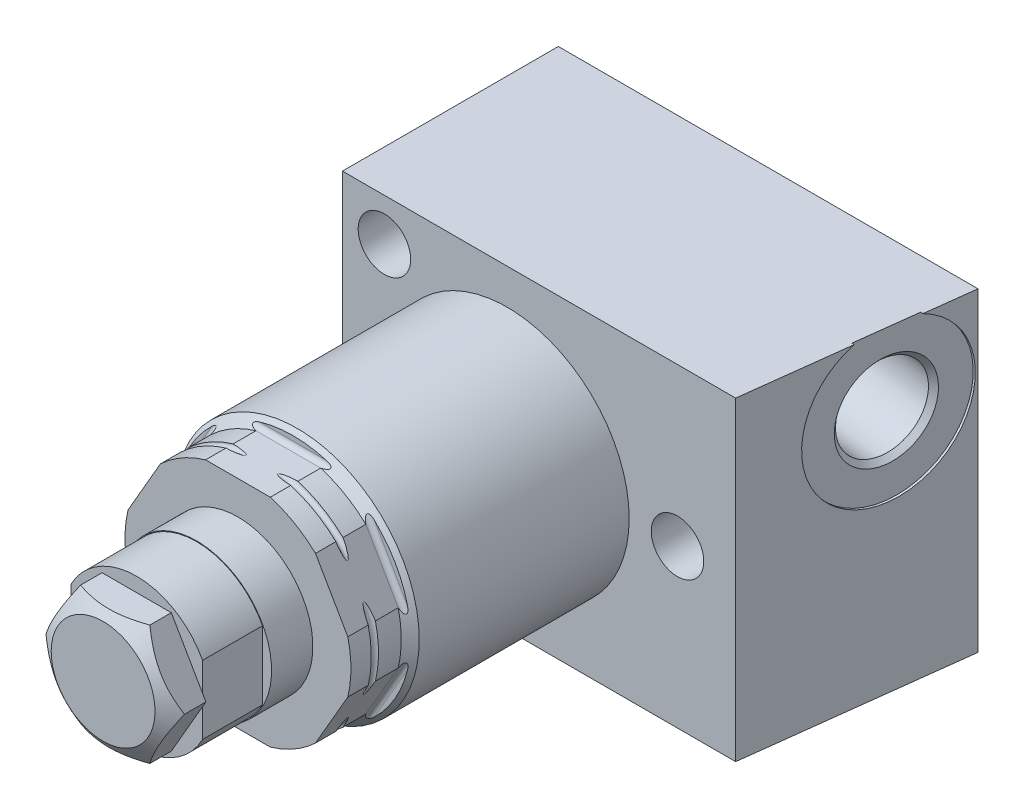
SolidWorks part; units mm, degrees
material "Alloy Steel"
ref_plane "Front Plane" through (0, 0, 0) normal (0, 0, 1) x (1, 0, 0)
ref_plane "Top Plane" through (0, 0, 0) normal (0, 1, 0) x (1, 0, 0)
ref_plane "Right Plane" through (0, 0, 0) normal (1, 0, 0) x (0, 0, -1)
sketch "Sketch1" plane through (0, 0, 0) normal (1, 0, 0) x (0, 0, -1)
  line L0 (0, 0) -> (122.3375, 0) construction
  line L1 (0, 0) -> (0, 11.6713)
  line L6 (0, 11.6713) -> (-7.112, 11.6713)
  line L7 (-7.112, 11.6713) -> (-8.3566, 12.9159)
  line L8 (-8.3566, 12.9159) -> (-35.8267, 12.9159)
  line L9 (-35.8267, 12.9159) -> (-36.7792, 11.9634)
  line L10 (-36.7792, 11.9634) -> (-42.1132, 11.9634)
  line L11 (-42.1132, 11.9634) -> (-42.1132, 0)
  line L12 (0, 0) -> (-42.1132, 0)
  dimension "D5" = 23.3426
  dimension "D6" = 7.112
  dimension "D7" = 25.8318
  dimension "D8" = 45
  dimension "D9" = 42.1132
  dimension "D10" = 23.9268
  dimension "D11" = 45
  dimension "D12" = 5.334
revolve "Revolve1" add sketch "Sketch1" angle 360 about L0
sketch "Sketch2" plane through (0, 0, 0) normal (1, 0, 0) x (0, 0, -1)
  line L0 (0, 0) -> (-47.105, 0) construction
  line L1 (-42.1132, 11.4617) -> (-36.7792, 11.4617)
  line L2 (-42.1132, 11.9634) -> (-42.1132, -11.9634) construction
  line L3 (-36.2712, 11.9697) -> (-36.2712, 14.6367)
  line L4 (-36.2712, 14.6367) -> (-42.1132, 14.6367)
  line L5 (-42.1132, 14.6367) -> (-42.1132, 11.4617)
  arc A0 (-36.2712, 11.9697) -> (-36.7792, 11.4617) centre (-36.7792, 11.9697) cw
  dimension "D4" = 0.508
  dimension "D1" = 22.9235
  dimension "D2" = 5.842
  dimension "D3" = 3.175
extrude "Cut-Extrude1" cut sketch "Sketch2" against normal through all and the other way through all
pattern_circular "CirPattern1" count 6 over 360 about axis through (0, 0, 0) along (0, 0, 1) of "Cut-Extrude1"
sketch "Sketch6" plane through (0, 0, 0) normal (0, 1, 0) x (1, 0, 0)
  line L0 (-17.4498, -13.5932) -> (24.1933, -13.5932)
  line L1 (24.1933, -13.5932) -> (27.0002, 9.2668)
  line L2 (27.0002, 9.2668) -> (-17.4498, 9.2668)
  line L3 (-17.4498, 9.2668) -> (-17.4498, -13.5932)
  line L4 (3.428, -42.1132) -> (-3.428, -42.1132) construction
  dimension "D1" = 28.52
  dimension "D2" = 83
  dimension "D3" = 22.86
  dimension "D4" = 44.45
  dimension "D5" = 17.4498
extrude "Extrude1" add sketch "Sketch6" along normal mid plane 33.3502
sketch "Sketch3" plane through (0, 0, 0) normal (1, 0, 0) x (0, 0, -1)
  line L0 (0, 0) -> (-60.8041, 0) construction
  line L1 (-56.3932, 0) -> (-56.3932, 7.9375) construction
  line L2 (-52.8372, 7.9375) -> (-42.1132, 7.9375)
  line L3 (-42.1132, 2.7621) -> (-42.1132, 8.6996) construction
  line L4 (-42.1132, 7.9375) -> (-42.1132, 0)
  line L5 (-42.1132, 2.7621) -> (-42.1132, -2.7621) construction
  line L6 (-42.1132, 0) -> (-52.8372, 0)
  line L7 (-52.8372, 7.9375) -> (-52.8372, 0)
  line L9 (9.2668, 16.6751) -> (9.2668, -16.6751) construction
  dimension "D1" = 3.556
  dimension "D2" = 15.875
  dimension "D3" = 65.66
revolve "Revolve2" add sketch "Sketch3" angle 360 about L0
sketch "Sketch4" plane through (0, 0, 52.8372) normal (0, 0, 1) x (1, 0, 0)
  circle A0 centre (0, 0) radius 3.0226
  circle A1 centre (0, 0) radius 7.9375 construction
  dimension "D1" = 6.0452
extrude "Cut-Extrude2" cut sketch "Sketch4" against normal blind 8.001
sketch "Sketch5" plane through (0, 0, 0) normal (1, 0, 0) x (0, 0, -1)
  line L0 (-42.1132, 11.4617) -> (-42.1132, 8.6996) construction
  line L1 (0, 0) -> (-52.6213, 0) construction
  line L2 (-39.9542, 15.1384) -> (-39.9542, 11.9634)
  line L3 (-39.1922, 15.1384) -> (-39.1922, 11.9634)
  line L4 (-39.9542, 15.1384) -> (-39.1922, 15.1384)
  arc A0 (-39.9542, 11.9634) -> (-39.1922, 11.9634) centre (-39.5732, 11.9634) ccw
  dimension "D3" = 0.762
  dimension "D1" = 2.54
  dimension "D2" = 11.9634
  dimension "D4" = 3.175
revolve "Cut-Revolve1" cut sketch "Sketch5" angle 360 about L1
hole_wizard "Hole1" positions "Sketch8" profile "Sketch7" legacy end condition up to next
sketch "Sketch8" plane through (0, 0, 13.5932) normal (0, 0, 1) x (1, 0, 0)
  line L0 (0, 0) -> (0, 25.169) construction
  line L1 (0, 0) -> (-25.7102, 0) construction
  point P0 (-13.0048, 12.192)
  point P9 (-13.0048, -12.192)
  point P10 (18.034, 0)
  dimension "D1" = 12.192
  dimension "D2" = 13.0048
  dimension "D3" = 18.034
sketch "Sketch7" plane through (-13.0048, 12.192, 13.5932) normal (1, 0, 0) x (0, -1, 0)
  line L0 (0, 0) -> (0, 22.86)
  line L1 (0, 22.86) -> (2.7813, 22.86)
  line L2 (2.7813, 22.86) -> (2.7813, 0)
  line L3 (2.7813, 0) -> (0, 0)
  line L4 (0, 110) -> (0, -10) construction
  dimension "Diameter" = 5.5626
  dimension "Depth" = 22.86
ref_plane "Plane1" through (0, 9.0932, 0) normal (0, 1, 0) x (-1, 0, 0)
sketch "Sketch9" plane through (0, 9.0932, 0) normal (0, 1, 0) x (-1, 0, 0)
  line L0 (-25.9632, -0.8212) -> (-18.705, -1.7124) construction
  line L1 (-24.1933, 13.5932) -> (-27.0002, -9.2668) construction
  line L2 (-24.9572, 7.3722) -> (-24.7051, 7.3413)
  line L3 (-24.7051, 7.3413) -> (-25.1075, 4.0639)
  line L4 (-25.1075, 4.0639) -> (-24.6431, 3.4695)
  line L5 (-24.6431, 3.4695) -> (-14.6849, 2.2468)
  line L6 (-14.6849, 2.2468) -> (-15.2235, -2.1399)
  line L7 (-15.2235, -2.1399) -> (-25.9632, -0.8212)
  line L8 (-25.9632, -0.8212) -> (-24.9572, 7.3722)
  dimension "D1" = 8.509
  dimension "D2" = 16.51
  dimension "D3" = 0.254
  dimension "D4" = 8.8392
  dimension "D5" = 10.5664
  dimension "D6" = 45
  dimension "D7" = 9.906
revolve "Cut-Revolve2" cut sketch "Sketch9" angle 360 about L0
sketch "Sketch10" plane through (0, 0, 0) normal (0, 1, 0) x (1, 0, 0)
  line L0 (0, 0) -> (0, -56.3853) construction
  line L1 (7.9375, -52.8372) -> (7.9375, -42.1132) construction
  line L2 (6.9723, -52.8372) -> (7.9375, -52.8372)
  line L3 (6.9723, -52.8372) -> (6.9723, -46.4872)
  line L4 (6.9723, -46.4872) -> (7.9375, -46.4872)
  line L5 (7.9375, -52.8372) -> (7.9375, -46.4872)
  line L6 (-7.9375, -52.8372) -> (7.9375, -52.8372) construction
  line L7 (-7.9375, -52.8372) -> (-7.9375, -46.4872)
  line L8 (-6.9723, -46.4872) -> (-7.9375, -46.4872)
  line L9 (-6.9723, -52.8372) -> (-6.9723, -46.4872)
  line L10 (-6.9723, -52.8372) -> (-7.9375, -52.8372)
  dimension "D1" = 13.9446
  dimension "D2" = 6.35
extrude "Cut-Extrude3" cut sketch "Sketch10" against normal through all and the other way through all
sketch "Sketch11" plane through (0, 0, 52.8372) normal (0, 0, 1) x (1, 0, 0)
  line L1 (3.6662, 6.35) -> (-3.6662, 6.35)
  line L2 (-3.6662, 6.35) -> (-7.3323, 0)
  line L3 (-7.3323, 0) -> (-3.6662, -6.35)
  line L4 (-3.6662, -6.35) -> (3.6662, -6.35)
  line L5 (3.6662, -6.35) -> (7.3323, 0)
  line L6 (7.3323, 0) -> (3.6662, 6.35)
  circle A0 centre (0, 0) radius 6.35 construction
  dimension "D1" = 12.7
extrude "Extrude2" add sketch "Sketch11" along normal blind 3.556
sketch "Sketch12" plane through (0, 0, 0) normal (0, 1, 0) x (1, 0, 0)
  line L0 (-7.3323, -55.1095) -> (-7.3323, -56.3932)
  line L1 (-7.3323, -56.3932) -> (-7.3323, -52.8372) construction
  line L2 (-7.3323, -56.3932) -> (-5.4991, -56.3932)
  line L3 (-3.6662, -56.3932) -> (-7.3323, -56.3932) construction
  line L4 (-5.4991, -56.3932) -> (-7.3323, -55.1095)
  line L5 (0, 0) -> (0, -66.9815) construction
  dimension "D1" = 35
  dimension "D2" = 10.9982
revolve "Cut-Revolve3" cut sketch "Sketch12" angle 360 about L5
sketch "Sketch13" plane through (0, 0, -9.2668) normal (0, 0, -1) x (-1, 0, 0)
  circle A0 centre (-17.4752, -9.7155) radius 6.35
  dimension "D1" = 12.7
  dimension "D2" = 17.4752
  dimension "D3" = 9.7155
extrude "Cut-Extrude4" cut sketch "Sketch13" against normal blind 2.54
hole_wizard "Hole2" positions "Sketch15" profile "Sketch14" legacy
sketch "Sketch15" plane through (0, 0, -6.7268) normal (0, 0, -1) x (-1, 0, 0)
  circle A0 centre (-17.4752, -9.7155) radius 6.35 construction
  point P0 (-17.4752, -9.7155)
sketch "Sketch14" plane through (17.4752, -9.7155, -6.7268) normal (1, 0, 0) x (0, 1, 0)
  line L0 (0, 0) -> (0, 14.2676)
  line L1 (0, 14.2676) -> (3.4544, 12.192)
  line L2 (3.4544, 12.192) -> (3.4544, 0)
  line L4 (3.4544, 0) -> (0, 0)
  line L6 (0, 14.2676) -> (-3.4544, 12.192) construction
  line L7 (0, -4.2442) -> (0, 117.3081) construction
  dimension "Diameter" = 6.9088
  dimension "Depth" = 12.192
  dimension "Drill Angle" = 118
ref_plane "Plane2" through (0, -9.7155, 0) normal (0, -1, 0) x (1, 0, 0)
sketch "Sketch16" plane through (0, -9.7155, 0) normal (0, -1, 0) x (1, 0, 0)
  line L0 (17.4752, 7.5408) -> (17.4752, -19.6513) construction
  line L1 (27.0002, -9.2668) -> (-17.4498, -9.2668) construction
  circle A0 centre (22.5552, -7.9968) radius 1.27
  dimension "D1" = 2.54
  dimension "D2" = 10.16
  dimension "D3" = 1.27
revolve "Revolve3" add sketch "Sketch16" angle 360 about L0
sketch "Sketch17" plane through (0, 0, 0) normal (1, 0, 0) x (0, 0, -1)
  line L0 (9.2668, 0) -> (-56.3932, 0) construction
  line L1 (9.2668, 16.6751) -> (9.2668, -16.6751) construction
  line L2 (-56.3932, 5.4991) -> (-56.3932, -5.4991) construction
  line L3 (-52.8372, 7.86) -> (-46.4872, 7.86)
  line L4 (-52.8372, 7.9375) -> (-52.8372, 3.7935) construction
  line L5 (-46.4872, 7.86) -> (-46.4872, 7.9375)
  line L6 (-42.1132, 7.9375) -> (-52.8372, 7.9375) construction
  line L7 (-46.4872, 7.9375) -> (-52.8372, 7.9375)
  line L8 (-52.8372, 7.9375) -> (-52.8372, 7.86)
  dimension "D1" = 6.35
  dimension "D2" = 15.72
revolve "Cut-Revolve4" cut sketch "Sketch17" angle 360 about L0
